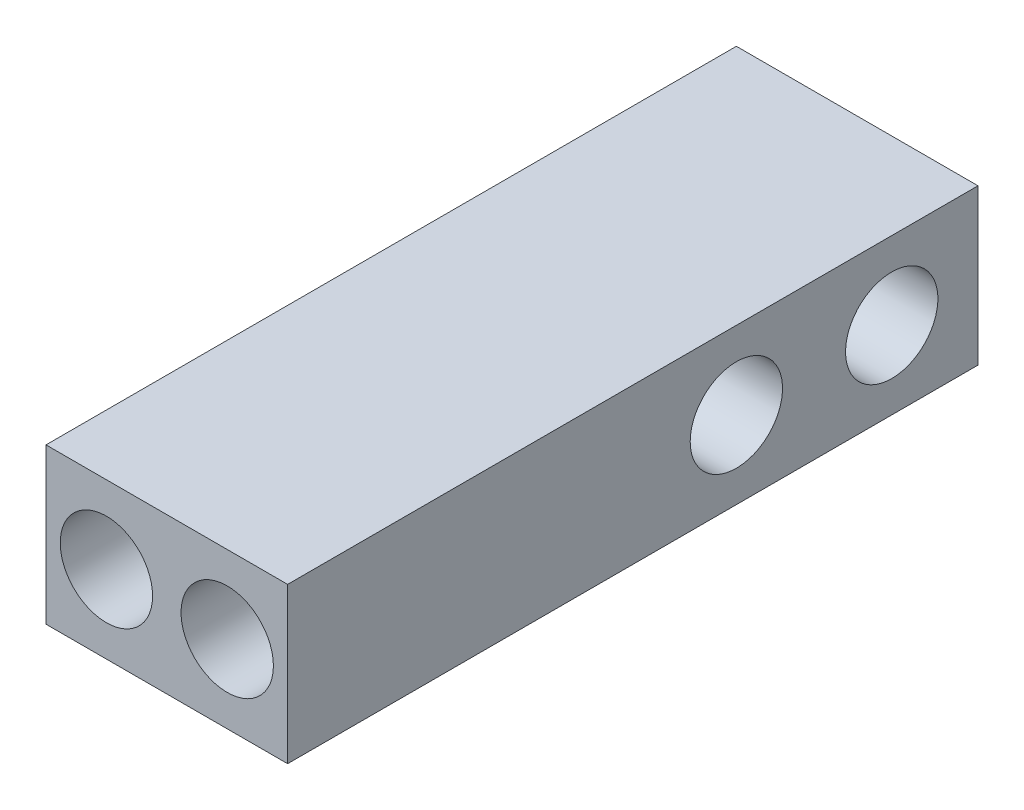
SolidWorks part; units mm, degrees
ref_plane "Alzado" through (0, 0, 0) normal (0, 0, 1) x (1, 0, 0)
ref_plane "Planta" through (0, 0, 0) normal (0, 1, 0) x (1, 0, 0)
ref_plane "Vista lateral" through (0, 0, 0) normal (1, 0, 0) x (0, 0, -1)
sketch "Croquis1" plane through (0, 0, 0) normal (0, 1, 0) x (1, 0, 0)
  line L1 (-7, -20) -> (7, -20)
  line L2 (-7, -20) -> (-7, 20)
  line L3 (-7, 20) -> (7, 20)
  line L4 (7, -20) -> (7, 20)
  line L5 (-7, -20) -> (7, 20) construction
  line L6 (-7, 20) -> (7, -20) construction
  point P0 (0, 0)
  dimension "D1" = 14
  dimension "D2" = 40
extrude "Saliente-Extruir1" add sketch "Croquis1" along normal blind 9
sketch "Croquis3" plane through (0, 0, 20) normal (0, 0, 1) x (1, 0, 0)
  line L0 (-3.5, 4.5) -> (0, 4.5) construction
  line L1 (-3.5, 4.5) -> (-7, 4.5) construction
  line L2 (0, 0) -> (0, 4.5) construction
  line L3 (-7, 9) -> (-7, 0) construction
  line L4 (0, 4.5) -> (3.5, 4.5) construction
  line L5 (7, 9) -> (7, 0) construction
  line L6 (7, 4.5) -> (3.5, 4.5) construction
  circle A0 centre (-3.5, 4.5) radius 2.675
  circle A1 centre (3.5, 4.5) radius 2.675
  dimension "D1" = 5.35
extrude "Cortar-Extruir2" cut sketch "Croquis3" against normal blind 15
sketch "Croquis4" plane through (-7, 0, 0) normal (-1, 0, 0) x (0, 0, 1)
  line L0 (-15, 4.5) -> (-6, 4.5) construction
  line L1 (-15, 4.5) -> (-20, 4.5) construction
  line L2 (-20, 9) -> (-20, 0) construction
  circle A0 centre (-15, 4.5) radius 2.675
  circle A1 centre (-6, 4.5) radius 2.675
  dimension "D1" = 5.35
  dimension "D2" = 9
  dimension "D3" = 5
extrude "Cortar-Extruir3" cut sketch "Croquis4" against normal through all
